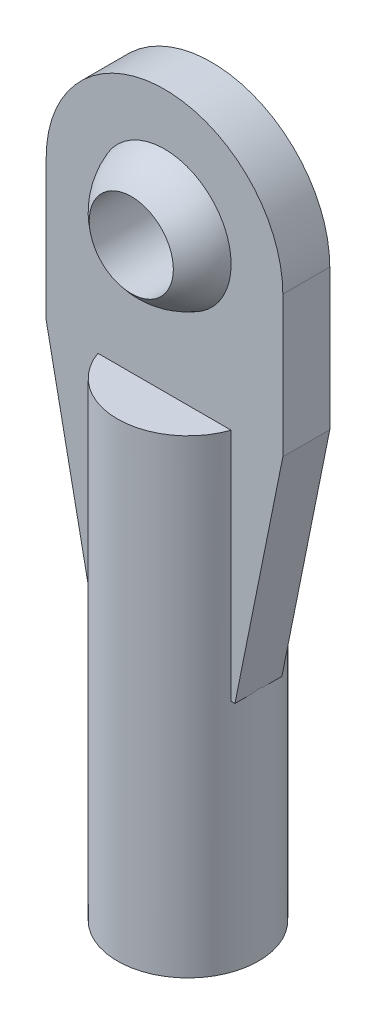
SolidWorks part; units mm, degrees
ref_plane "Front Plane" through (0, 0, 0) normal (0, 0, 1) x (1, 0, 0)
ref_plane "Top Plane" through (0, 0, 0) normal (0, 1, 0) x (1, 0, 0)
ref_plane "Right Plane" through (0, 0, 0) normal (1, 0, 0) x (0, 0, -1)
sketch "Sketch2" plane through (0, 0, 0) normal (0, 0, 1) x (1, 0, 0)
  line L0 (0, 6.0439) -> (0, -6.9998) construction
  line L1 (0, 2.3876) -> (0, -2.3876)
  arc A0 (0, -2.3876) -> (0, 2.3876) centre (0, 0) ccw
  dimension "D1" = 4.7752
revolve "Revolve1" add sketch "Sketch2" angle 360 about L0
sketch "Sketch3" plane through (0, 0, 0) normal (0, 0, 1) x (1, 0, 0)
  circle A0 centre (0, 0) radius 1.4224
  dimension "D1" = 2.8448
extrude "Cut-Extrude1" cut sketch "Sketch3" against normal through all and the other way through all
sketch "Sketch4" plane through (0, 0, 0) normal (0, 0, 1) x (1, 0, 0)
  line L0 (-4.0005, 0) -> (-4.0005, -4.7625)
  line L1 (-4.0005, -4.7625) -> (-2.3812, -12.7953)
  line L2 (4.0005, -4.7625) -> (2.3813, -12.7953)
  line L3 (-2.3812, -12.7953) -> (2.3813, -12.7953)
  line L4 (0, -4.0005) -> (0, -21.59) construction
  line L5 (4.0005, 0) -> (4.0005, -4.7625)
  arc A0 (4.0005, 0) -> (-4.0005, 0) centre (0, 0) ccw
  circle A1 centre (0, 0) radius 1.4224 construction
  circle A2 centre (0, 0) radius 1.4224
  point P9 (0, -12.7952)
  dimension "D1" = 8.001
  dimension "D2" = 21.59
  dimension "D3" = 4.7625
  dimension "D4" = 4.7625
extrude "Boss-Extrude1" add sketch "Sketch4" along normal mid plane 1.5875
sketch "Sketch5" plane through (0, -12.7953, 0) normal (0, -1, 0) x (1, 0, 0)
  circle A0 centre (0, 0) radius 2.3876
  arc A1 (2.2518, 0.7937) -> (1.4224, 1.9177) centre (0, 0) ccw construction
extrude "Boss-Extrude2" add sketch "Sketch5" against normal mid plane 15.875
hole_wizard "#4-40 Tapped Hole1" positions "Sketch7" profile "Sketch6" tap size "#4-40" standard "ANSI Inch"
sketch "Sketch7" plane through (0, -20.7328, 0) normal (0, -1, 0) x (-1, 0, 0)
  point P0 (0, 0)
sketch "Sketch6" plane through (0, -20.7328, 0) normal (1, 0, 0) x (0, 0, -1)
  line L0 (0, 0) -> (0, 13.3792)
  line L1 (0, 13.3792) -> (1.1303, 12.7)
  line L2 (1.1303, 12.7) -> (1.1303, 0)
  line L5 (1.1303, 0) -> (0, 0)
  line L10 (0, 13.3792) -> (-1.1303, 12.7) construction
  line L11 (0, -6.35) -> (0, 107.95) construction
  dimension "Tap Drill Dia." = 2.2606
  dimension "Tap Drill Depth" = 12.7
  dimension "Drill Angle" = 118
